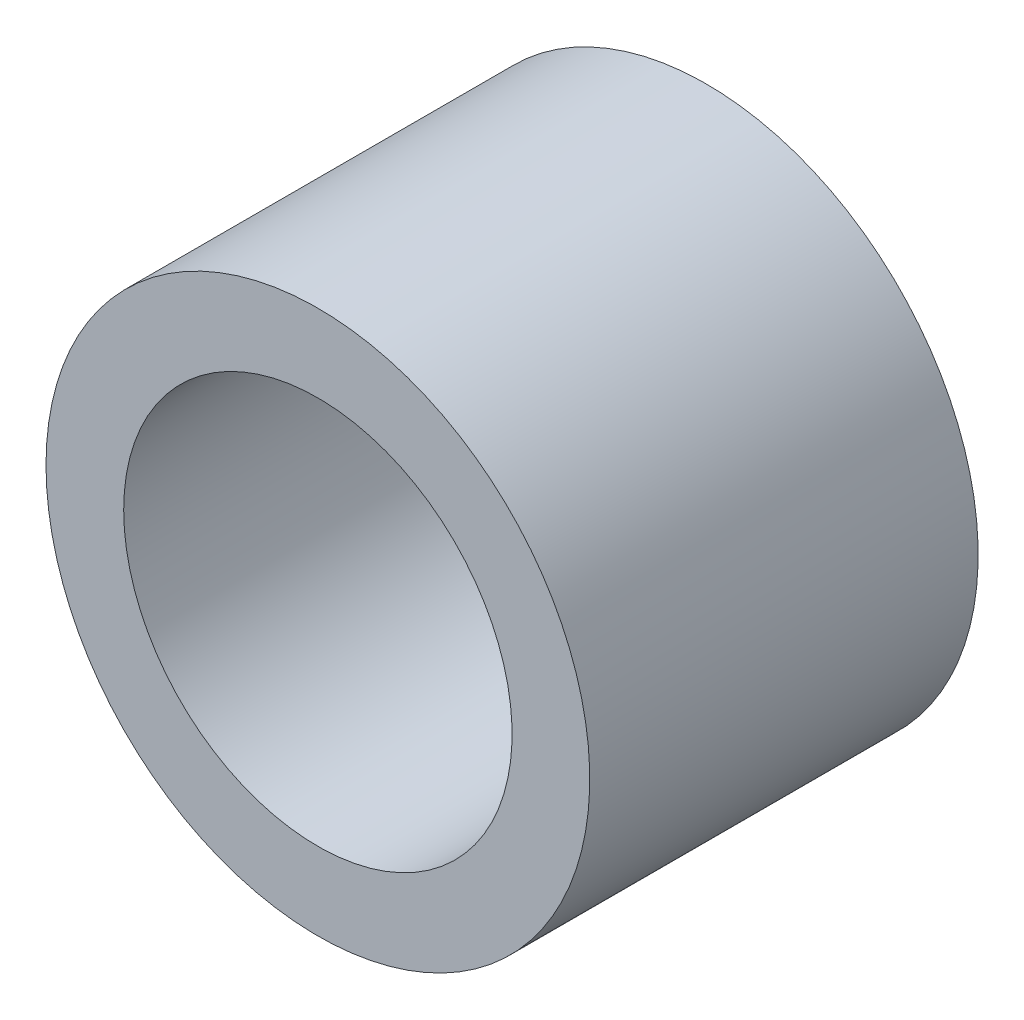
SolidWorks part; units mm, degrees
material "ABS"
ref_plane "Front Plane" through (0, 0, 0) normal (0, 0, 1) x (1, 0, 0)
ref_plane "Top Plane" through (0, 0, 0) normal (0, 1, 0) x (1, 0, 0)
ref_plane "Right Plane" through (0, 0, 0) normal (1, 0, 0) x (0, 0, -1)
sketch "Sketch1" plane through (0, 0, 0) normal (0, 1, 0) x (1, 0, 0)
  line L0 (0, 12.6365) -> (0, -14.3867) construction
  line L1 (0, 4) -> (2, 4)
  line L2 (2, 4) -> (2, 5)
  line L3 (2, 5) -> (7, 5)
  line L4 (7, 5) -> (7, -5)
  line L5 (7, -5) -> (5, -5)
  line L6 (5, -5) -> (5, 3)
  line L7 (5, 3) -> (0, 3)
  line L8 (0, 4) -> (0, 3)
  point P5 (7, 0)
  dimension "D1" = 10
  dimension "D2" = 8
  dimension "D3" = 4
  dimension "D4" = 1
  dimension "D5" = 10
  dimension "D6" = 14
revolve "Revolve1" add sketch "Sketch1" angle 360 about L0
sketch "Sketch2" plane through (0, 0, -4) normal (0, 0, -1) x (-1, 0, 0)
  circle A0 centre (0, 0) radius 2
extrude "Cut-Extrude1" [suppressed] cut sketch "Sketch2" against normal blind 10
